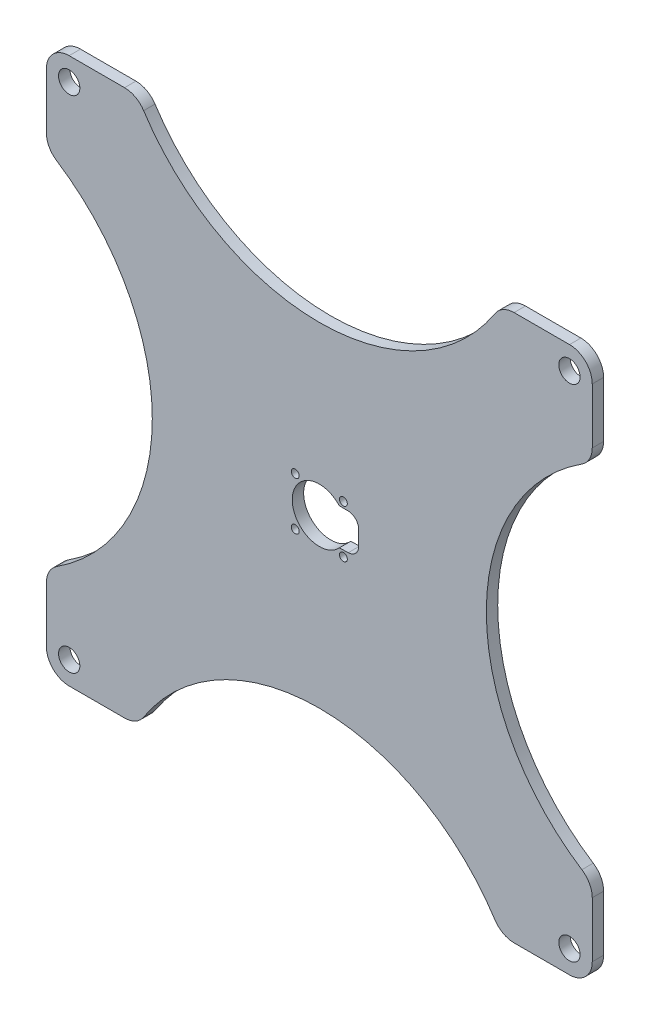
SolidWorks part; units mm, degrees
ref_plane "Front Plane" through (0, 0, 0) normal (0, 0, 1) x (1, 0, 0)
ref_plane "Top Plane" through (0, 0, 0) normal (0, 1, 0) x (1, 0, 0)
ref_plane "Right Plane" through (0, 0, 0) normal (1, 0, 0) x (0, 0, -1)
sketch "Sketch3" plane through (0, 0, 0) normal (0, 0, 1) x (1, 0, 0)
  line L1 (-76.2, -76.2) -> (76.2, -76.2)
  line L2 (-76.2, -76.2) -> (-76.2, 76.2)
  line L3 (-76.2, 76.2) -> (76.2, 76.2)
  line L4 (76.2, -76.2) -> (76.2, 76.2)
  line L5 (-76.2, -76.2) -> (76.2, 76.2) construction
  line L6 (-76.2, 76.2) -> (76.2, -76.2) construction
  point P0 (0, 0)
  dimension "D1" = 152.4
extrude "Boss-Extrude3" add sketch "Sketch3" along normal blind 3.175
sketch "Sketch13" plane through (0.1069, -2.0309, 3.175) normal (0, 0, 1) x (1, 0, 0)
  line L0 (10.8931, 2.1056) -> (16.2467, 2.1056) construction
  line L1 (-76.3069, 78.2309) -> (76.0931, -74.1691) construction
  line L4 (5.4833, 7.1056) -> (10.8931, 7.1056)
  line L5 (10.8931, -2.8944) -> (10.8931, 7.1056)
  line L7 (5.4833, -3.0438) -> (10.8931, -2.8944)
  line L16 (-76.3069, -74.1691) -> (76.0931, 78.2309) construction
  arc A1 (5.4833, 7.1056) -> (5.4833, -3.0438) centre (-0.1069, 2.0309) ccw
  point P6 (0, 0)
  point P8 (0, 0)
  dimension "D1" = 5.5902
  dimension "D4" = 10
  dimension "D3" = 7.55
  dimension "D2" = 5.5902
  dimension "D5" = 11
extrude "Motor Cut Out" cut sketch "Sketch13" against normal through all
sketch "Sketch20" plane through (0, 0, 3.175) normal (0, 0, 1) x (1, 0, 0)
  line L1 (-69.83, -69.83) -> (69.83, -69.83) construction
  line L2 (-69.83, -69.83) -> (-69.83, 69.83) construction
  line L3 (-69.83, 69.83) -> (69.83, 69.83) construction
  line L4 (69.83, -69.83) -> (69.83, 69.83) construction
  line L5 (-69.83, -69.83) -> (69.83, 69.83) construction
  line L6 (-69.83, 69.83) -> (69.83, -69.83) construction
  circle A0 centre (-69.83, 69.83) radius 2.9718
  circle A1 centre (69.83, 69.83) radius 2.9718
  circle A2 centre (69.83, -69.83) radius 2.9718
  circle A3 centre (-69.83, -69.83) radius 2.9718
  point P0 (0, 0)
  point P11 (0, 0)
  dimension "D1" = 4
  dimension "D2" = 139.66
  dimension "D3" = 5.9436
extrude "Bolt Holes" cut sketch "Sketch20" against normal through all both and the other way through all
sketch "Sketch21" plane through (0, 0, 3.175) normal (0, 0, 1) x (1, 0, 0)
  line L1 (-39.6561, -36.877) -> (39.6561, -36.877)
  line L2 (-39.6561, -36.877) -> (-39.6561, 36.877)
  line L3 (-39.6561, 36.877) -> (39.6561, 36.877)
  line L4 (39.6561, -36.877) -> (39.6561, 36.877)
  line L5 (-39.6561, -36.877) -> (39.6561, 36.877) construction
  line L6 (-39.6561, 36.877) -> (39.6561, -36.877) construction
  point P0 (0, 0)
ref_plane "Mirror" through (0, 0, 0) normal (0.7071, -0.7071, 0) x (-0.7071, -0.7071, 0)
sketch "Sketch25" plane through (0, 0, 3.175) normal (0, 0, 1) x (1, 0, 0)
  line L0 (-76.2, 76.2) -> (-76.2, -76.2) construction
  line L1 (76.2, 76.2) -> (-76.2, 76.2) construction
  line L2 (-76.2, -76.2) -> (76.2, -76.2) construction
  line L3 (-76.2, 50.8) -> (-76.2, -50.8)
  arc A0 (-76.2, 50.8) -> (-76.2, -50.8) centre (-105.0489, 0) cw
  dimension "D3" = 58.42
  dimension "D1" = 25.4
  dimension "D2" = 25.4
extrude "Edge cut out" cut sketch "Sketch25" against normal up to surface (3.175 mm away) up to face at (-66.8582, -69.83, 0)
fillet "Fillet2" radius 6.35 4 edges at (-76.2, -76.2, 1.5875) (-76.2, -50.8, 1.5875) (-76.2, 50.8, 1.5875) (-76.2, 76.2, 1.5875)
ref_plane "Plane3" through (0, 0, 0) normal (-0.7071, -0.7071, 0) x (-0.7071, 0.7071, 0)
mirror "Mirror4" about plane through (0, 0, 0) normal (0.7071, -0.7071, 0) of "Edge cut out"
mirror "Mirror5" about plane through (0, 0, 0) normal (-0.7071, -0.7071, 0) of "Mirror4", "Edge cut out"
fillet "Fillet3" radius 6.35 6 edges at (76.2, 76.2, 1.5875) (76.2, 50.8, 1.5875) (76.2, -50.8, 1.5875) (76.2, -76.2, 1.5875) (50.8, -76.2, 1.5875) (-50.8, -76.2, 1.5875)
fillet "Fillet4" radius 6.35 2 edges at (-50.8, 76.2, 1.5875) (50.8, 76.2, 1.5875)
fillet "Fillet12" radius 3 2 edges at (11, 5.0747, 1.5875) (11, -4.9253, 1.5875)
sketch "Sketch27" plane through (0, 0, 3.175) normal (0, 0, 1) x (1, 0, 0)
  line L3 (-6.72, -6.72) -> (6.72, -6.72) construction
  line L4 (-6.72, -6.72) -> (-6.72, 6.72) construction
  line L5 (-6.72, 6.72) -> (6.72, 6.72) construction
  line L6 (6.72, -6.72) -> (6.72, 6.72) construction
  line L7 (-6.72, -6.72) -> (6.72, 6.72) construction
  line L8 (-6.72, 6.72) -> (6.72, -6.72) construction
  circle A5 centre (6.72, -6.72) radius 1.1
  circle A6 centre (6.72, 6.72) radius 1.1
  circle A9 centre (-6.72, 6.72) radius 1.1
  circle A10 centre (-6.72, -6.72) radius 1.1
  point P0 (0, 0)
  point P1 (0, 0)
  dimension "D1" = 13.44
  dimension "D8" = 2.2
extrude "Motor screws hole" cut sketch "Sketch27" against normal through all
